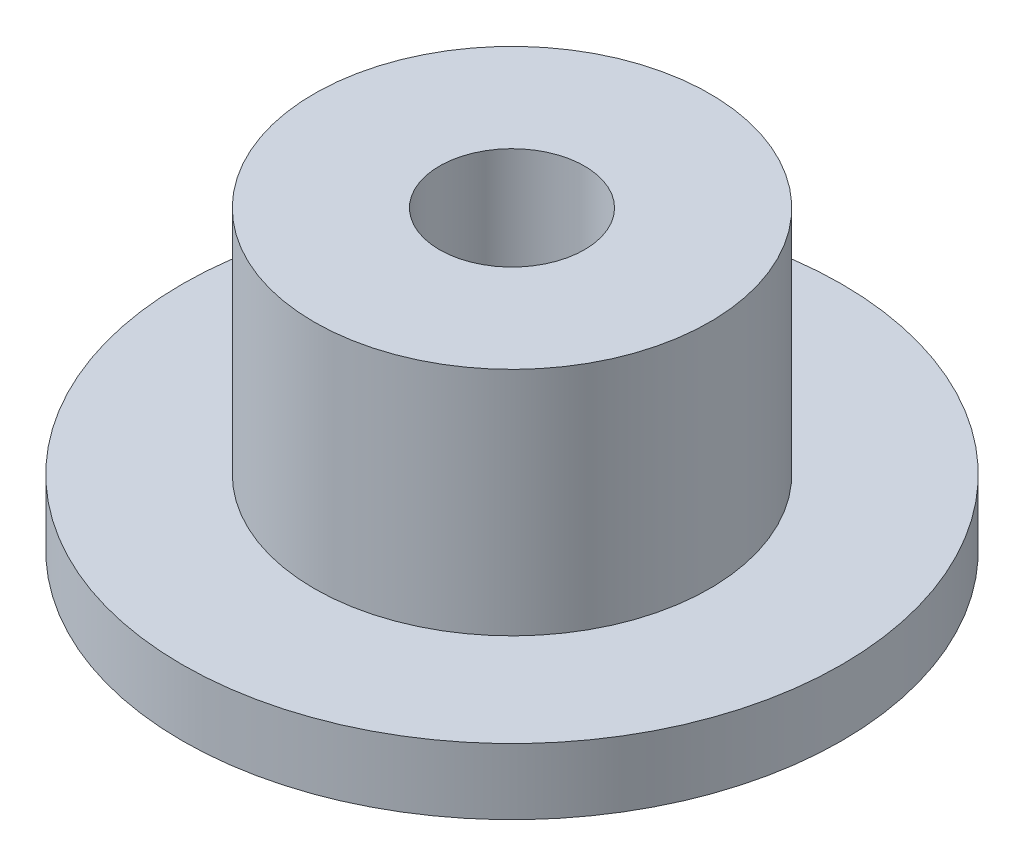
SolidWorks part; units mm, degrees
ref_plane "Alzado" through (0, 0, 0) normal (0, 0, 1) x (1, 0, 0)
ref_plane "Planta" through (0, 0, 0) normal (0, 1, 0) x (1, 0, 0)
ref_plane "Vista lateral" through (0, 0, 0) normal (1, 0, 0) x (0, 0, -1)
sketch "Croquis1" plane through (0, 0, 0) normal (0, 0, 1) x (1, 0, 0)
  line L0 (0, 11.7191) -> (0, -4.7066) construction
  line L1 (2.2, 9) -> (2.2, 3)
  line L2 (2.2, 3) -> (4.1, 3)
  line L3 (4.1, 3) -> (4.1, 0.6)
  line L4 (4.1, 0.6) -> (4.65, 0.6)
  line L5 (4.65, 0.6) -> (4.65, 0)
  line L6 (4.65, 0) -> (10, 0)
  line L7 (10, 0) -> (10, 2)
  line L8 (10, 2) -> (6, 2)
  line L9 (6, 2) -> (6, 9)
  line L10 (6, 9) -> (2.2, 9)
  point P13 (0, 0)
  point P14 (0, 10.6323)
  point P15 (0, 11.7191)
  dimension "D1" = 2.2
  dimension "D2" = 6
  dimension "D3" = 9
  dimension "D4" = 3
  dimension "D5" = 0.6
  dimension "D6" = 10
  dimension "D7" = 4.65
  dimension "D8" = 4.1
  dimension "D9" = 2
revolve "Revolución1" add sketch "Croquis1" angle 360 about L0
